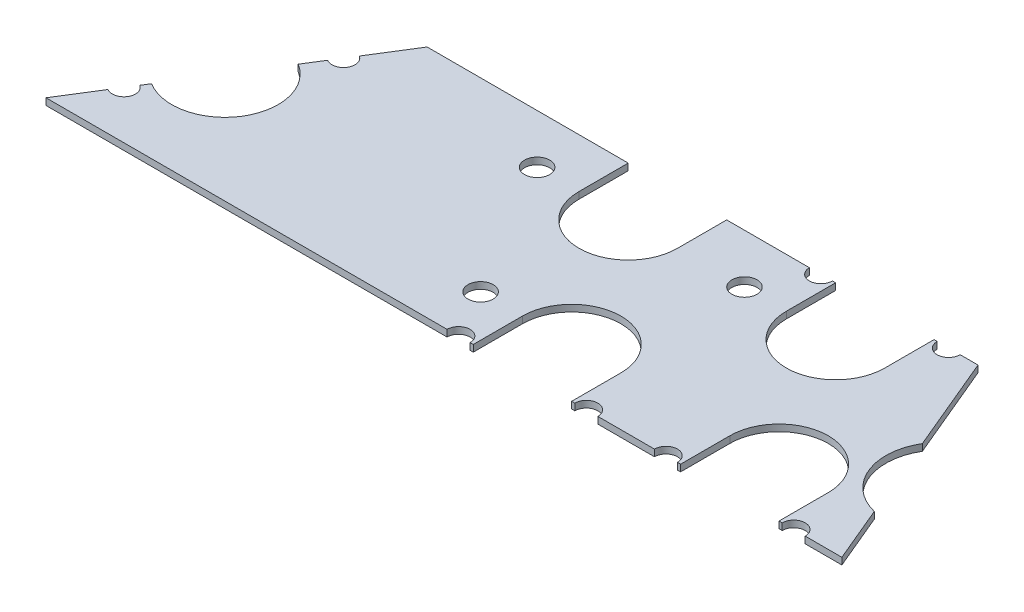
SolidWorks part; units mm, degrees
ref_plane "Front" through (0, 0, 0) normal (0, 0, 1) x (1, 0, 0)
ref_plane "Top" through (0, 0, 0) normal (0, 1, 0) x (1, 0, 0)
ref_plane "Right" through (0, 0, 0) normal (1, 0, 0) x (0, 0, -1)
sketch "Sketch1" plane through (0, 0, 0) normal (0, 1, 0) x (1, 0, 0)
  line L0 (0, 0) -> (190, 0)
  line L1 (190, 0) -> (166.5, 56)
  line L2 (166.5, 56) -> (35, 56)
  line L3 (35, 56) -> (0, 0)
  line L4 (83, 44.25) -> (83, 56)
  line L5 (106.5, 44.25) -> (106.5, 56)
  line L6 (132.5, 44.25) -> (132.5, 56)
  line L7 (156, 44.25) -> (156, 56)
  line L8 (102, 11.75) -> (102, 0)
  line L9 (125.5, 11.75) -> (125.5, 0)
  line L10 (151.5, 11.75) -> (151.5, 0)
  line L11 (175, 11.75) -> (175, 0)
  line L12 (113.75, 11.75) -> (163.25, 11.75) construction
  line L13 (94.75, 44.25) -> (144.25, 44.25) construction
  line L14 (94.75, 44.25) -> (73, 44.25) construction
  line L15 (92, 11.75) -> (113.75, 11.75) construction
  circle A0 centre (16.43, 26.2879) radius 12.7
  circle A1 centre (7.155, 11.448) radius 2.75
  circle A2 centre (98.5, 0) radius 2.75
  circle A3 centre (113.75, 11.75) radius 11.75
  circle A4 centre (163.25, 11.75) radius 11.75
  circle A5 centre (144.25, 44.25) radius 11.75
  circle A6 centre (94.75, 44.25) radius 11.75
  circle A7 centre (92, 11.75) radius 3
  circle A8 centre (73, 44.25) radius 3
  circle A9 centre (122.5, 44.25) radius 3
  circle A10 centre (129, 56) radius 2.75
  circle A11 centre (159.5, 56) radius 2.75
  circle A12 centre (187.5286, 26.2879) radius 13.3104
  circle A13 centre (178.5, 0) radius 2.75
  circle A14 centre (148, 0) radius 2.75
  circle A15 centre (129, 0) radius 2.75
  circle A16 centre (27.315, 43.704) radius 2.75
  point P55 (91.9401, 0)
  point P56 (122.7728, 0)
  point P57 (131.5363, 0)
  point P58 (102, 0)
  point P59 (118.4452, 0)
  point P60 (120.6261, 0)
  point P61 (146.2512, 0)
  point P62 (131.076, 0)
  point P63 (97.5453, 0)
  point P64 (178.8732, 0)
  point P65 (147.8868, 0)
  point P66 (129.2587, 0)
  point P67 (160.2216, 56)
  point P68 (128.3702, 56)
  point P69 (115.1659, 44.25)
  point P70 (123.7566, 44.25)
  point P71 (187.5286, 26.2879)
  dimension "D5" = 25.4
  dimension "D6" = 23.5
  dimension "D7" = 5.5
  dimension "D8" = 6
  dimension "D1" = 190
  dimension "D2" = 56
  dimension "D3" = 131.5
  dimension "D4" = 35
  dimension "D9" = 13.5
  dimension "D10" = 31
  dimension "D11" = 14.5
  dimension "D12" = 49.5
  dimension "D13" = 15
  dimension "D14" = 11.75
  dimension "D15" = 11.75
  dimension "D16" = 10.5
  dimension "D17" = 49.5
  dimension "D18" = 10
  dimension "D19" = 3.5
  dimension "D20" = 3.5
  dimension "D21" = 30.5
  dimension "D22" = 10
  dimension "D23" = 10
  dimension "D24" = 3.5
  dimension "D25" = 3.5
  dimension "D26" = 3.5
  dimension "D27" = 3.5
  dimension "D28" = 30.5
  dimension "D29" = 30.5
extrude "Boss-Extrude1" add sketch "Sketch1" along normal blind 1.6 contours A16 L3 A0 A1 L0 A2 L8 A3 L9 A15 A14 L10 A4 L11 A13 L1 A12 L2 A11 L7 A5 L6 A10 L5 A6 L4 A9 A8 A7
